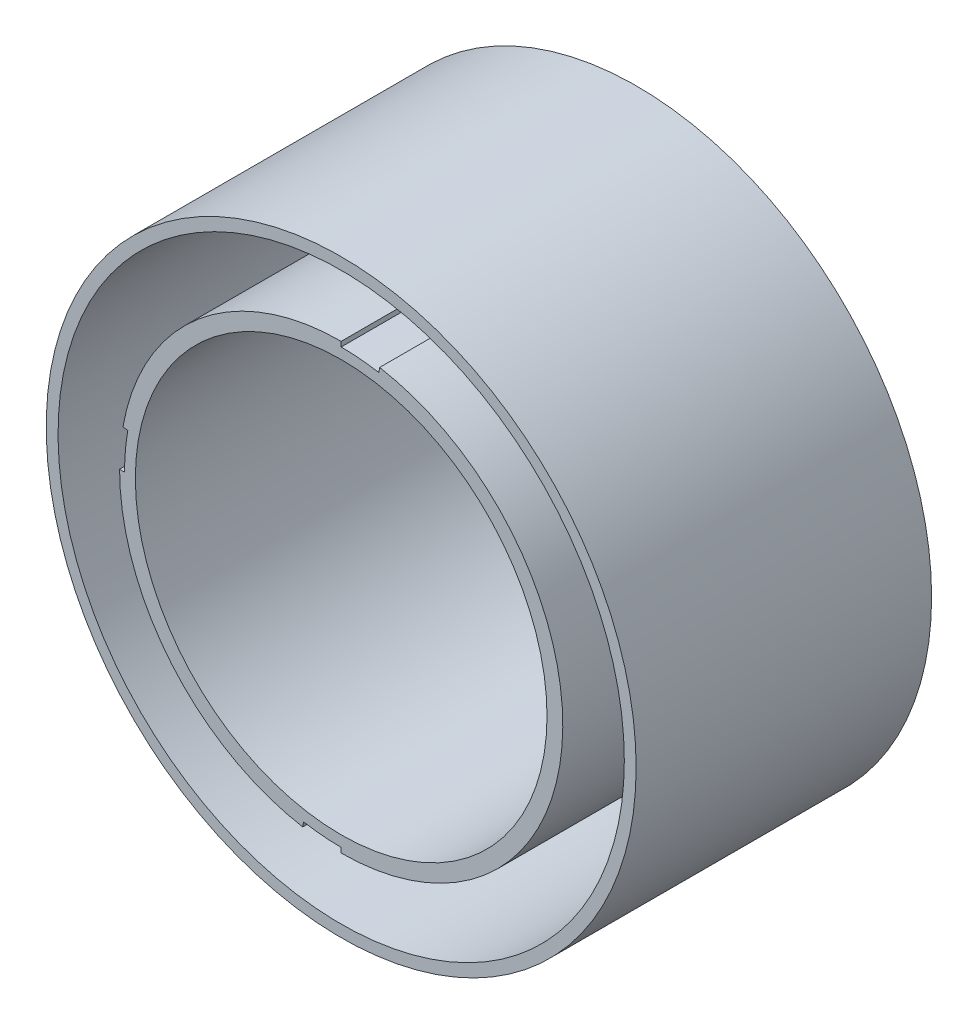
SolidWorks part; units mm, degrees
ref_plane "Alzado" through (0, 0, 0) normal (0, 0, 1) x (1, 0, 0)
ref_plane "Planta" through (0, 0, 0) normal (0, 1, 0) x (1, 0, 0)
ref_plane "Vista lateral" through (0, 0, 0) normal (1, 0, 0) x (0, 0, -1)
sketch "Croquis1" plane through (0, 0, 0) normal (0, 0, 1) x (1, 0, 0)
  circle A0 centre (0, 0) radius 22.5
  circle A1 centre (0, 0) radius 20.9
  circle A2 centre (0, 0) radius 28.75
  circle A3 centre (0, 0) radius 29.95
  dimension "D1" = 45
  dimension "D3" = 57.5
  dimension "D2" = 1.6
  dimension "D4" = 1.2
extrude "Saliente-Extruir1" add sketch "Croquis1" along normal blind 30 contours A0 A1 | A3 A2
sketch "Croquis2" plane through (0, 0, 30) normal (0, 0, 1) x (1, 0, 0)
  line L0 (0, 0) -> (0, 22.5) construction
  line L1 (0, 22.5) -> (0, 21.9998)
  line L2 (3.8202, 21.6656) -> (3.9071, 22.1582)
  line L3 (21.6656, -3.8202) -> (22.1582, -3.9071)
  line L4 (22.5, 0) -> (21.9998, 0)
  line L5 (-3.8202, -21.6656) -> (-3.9071, -22.1582)
  line L6 (0, -22.5) -> (0, -21.9998)
  line L7 (-21.6656, 3.8202) -> (-22.1582, 3.9071)
  line L8 (-22.5, 0) -> (-21.9998, 0)
  line L9 (0, 0) -> (3.8202, 21.6656) construction
  circle A0 centre (0, 0) radius 22.5 construction
  arc A1 (3.9071, 22.1582) -> (0, 22.5) centre (0, 0) ccw
  arc A3 (22.1582, -3.9071) -> (22.5, 0) centre (0, 0) ccw
  arc A4 (21.6656, -3.8202) -> (21.9998, 0) centre (0, 0) ccw
  arc A5 (-3.9071, -22.1582) -> (0, -22.5) centre (0, 0) ccw
  arc A6 (-3.8202, -21.6656) -> (0, -21.9998) centre (0, 0) ccw
  arc A7 (-22.1582, 3.9071) -> (-22.5, 0) centre (0, 0) ccw
  arc A8 (-21.6656, 3.8202) -> (-21.9998, 0) centre (0, 0) ccw
  arc A9 (0, 21.9998) -> (3.8202, 21.6656) centre (0, 0) cw
  point P24 (0, 0)
  circle M7 centre (0, 0) radius 22.5
  dimension "D2" = 10
  dimension "D1" = 21.9998
  dimension "D4" = 4
extrude "Cortar-Extruir1" cut sketch "Croquis2" against normal blind 30 contours L1 A9 L2 M7 | A6 L6 A5 L5 | A7 L8 A8 L7
sketch "Croquis3" plane through (0, 0, 0) normal (0, 0, -1) x (-1, 0, 0)
  line L0 (-29.95, 0) -> (29.95, 0) construction
  line L1 (0, 0) -> (21.1778, 21.1778) construction
  line L2 (0, -29.95) -> (0, 29.95) construction
  line L3 (23.8165, 18.1597) -> (-18.1597, -23.8165)
  line L4 (-18.1597, -23.8165) -> (-23.8165, -18.1597)
  line L5 (-23.8165, -18.1597) -> (18.1597, 23.8165)
  line L6 (18.1597, 23.8165) -> (23.8165, 18.1597)
  line L7 (-18.1597, 23.8165) -> (-23.8165, 18.1597)
  line L8 (23.8165, -18.1597) -> (-18.1597, 23.8165)
  line L9 (18.1597, -23.8165) -> (23.8165, -18.1597)
  line L10 (-23.8165, 18.1597) -> (18.1597, -23.8165)
  circle A0 centre (0, 0) radius 29.95 construction
  arc M12 (-3.9071, 22.1582) -> (0, -22.5) centre (0, 0) ccw
  arc M16 (-3.9071, 22.1582) -> (0, -22.5) centre (0, 0) ccw
  arc M20 (3.9071, -22.1582) -> (22.5, 0) centre (0, 0) ccw
  arc M24 (22.1582, 3.9071) -> (0, 22.5) centre (0, 0) ccw
  dimension "D1" = 45
  dimension "D2" = 8
extrude "Saliente-Extruir2" add sketch "Croquis3" against normal blind 4 contours L7 L10 L8 M12 | L5 L4 L3 M16 | L10 L9 L8 M20 | L6 L5 L3 M24
